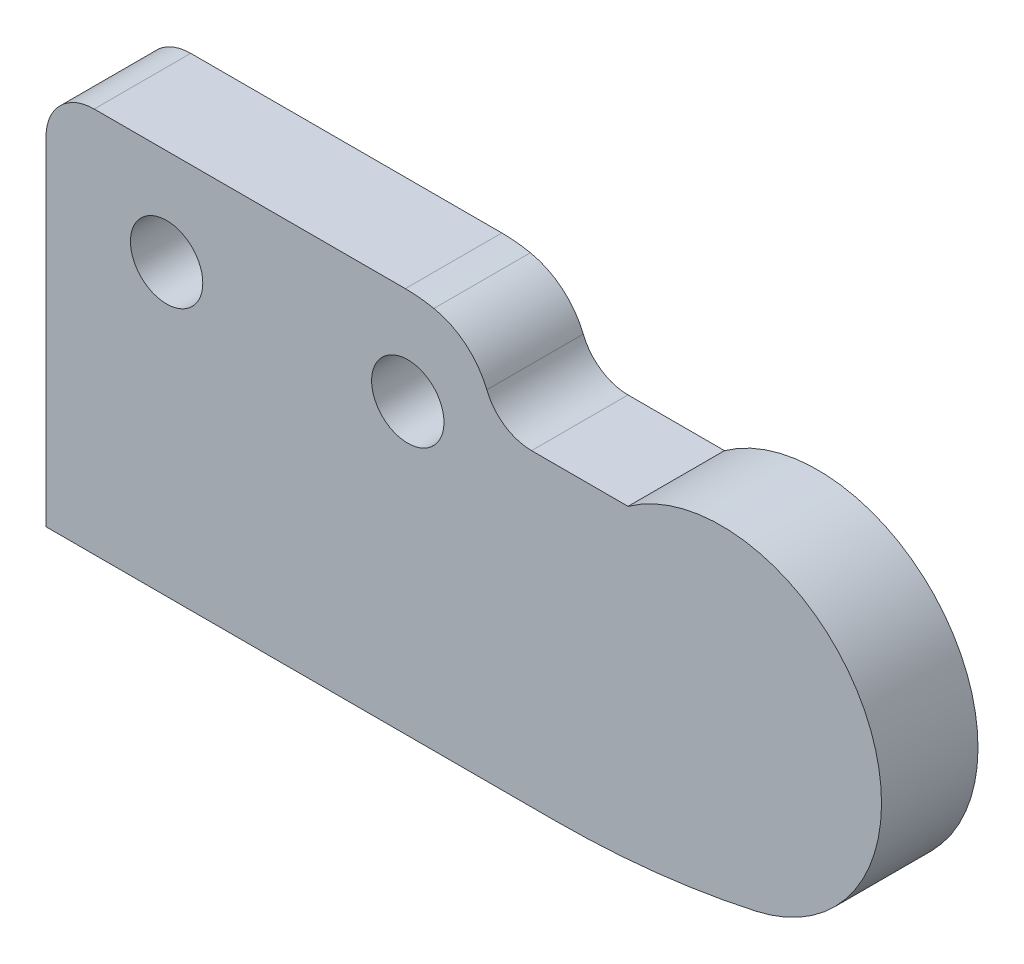
SolidWorks part; units mm, degrees
ref_plane "Front Plane" through (0, 0, 0) normal (0, 0, 1) x (1, 0, 0)
ref_plane "Top Plane" through (0, 0, 0) normal (0, 1, 0) x (1, 0, 0)
ref_plane "Right Plane" through (0, 0, 0) normal (1, 0, 0) x (0, 0, -1)
sketch "Sketch1" plane through (0, 0, 0) normal (0, 0, 1) x (1, 0, 0)
  line L0 (4.9488, 2) -> (-1.5, 2)
  line L1 (-2.5, 1) -> (-2.5, -6)
  line L2 (-2.5, -6) -> (8.0316, -6)
  line L3 (9.5661, 0.4) -> (7.5661, 0.4)
  line L4 (2.8303, 0.75) -> (6.7567, 0.75) construction
  circle A0 centre (0, 0) radius 0.75
  circle A1 centre (5, 0) radius 0.75
  arc A2 (-1.5, 2) -> (-2.5, 1) centre (-1.5, 1) ccw
  arc A5 (4.9488, 2) -> (5.542, 1.9408) centre (4.9488, -1) cw
  arc A6 (5.542, 1.9408) -> (6.6378, 1.0282) centre (5.2454, 0.4704) cw
  arc A7 (6.6378, 1.0282) -> (7.5661, 0.4) centre (7.5661, 1.4) ccw
  arc A8 (9.5661, 0.4) -> (12.217, -5.5428) centre (11.5, -2.3) cw
  arc A9 (12.217, -5.5428) -> (8.0316, -6) centre (8.0316, 13.3858) cw
  dimension "D1" = 1.5
  dimension "D2" = 1.5
  dimension "D8" = 3.3211
  dimension "D9" = 3
  dimension "D10" = 1.5
  dimension "D11" = 1
  dimension "D13" = 1
  dimension "D3" = 5
  dimension "D4" = 2
  dimension "D5" = 2.5
  dimension "D6" = 6
  dimension "D7" = 0.4
  dimension "D12" = 2
  dimension "D14" = 11.5
  dimension "D15" = 2.3
extrude "Boss-Extrude1" add sketch "Sketch1" along normal blind 2
